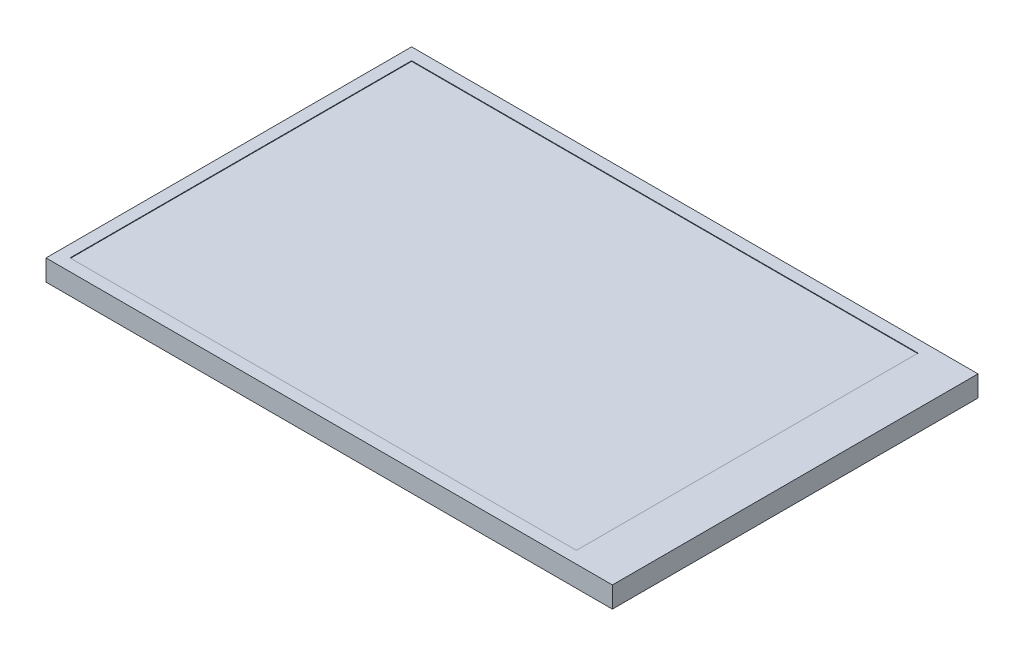
SolidWorks part; units mm, degrees
ref_plane "Front Plane" through (0, 0, 0) normal (0, 0, 1) x (1, 0, 0)
ref_plane "Top Plane" through (0, 0, 0) normal (0, 1, 0) x (1, 0, 0)
ref_plane "Right Plane" through (0, 0, 0) normal (1, 0, 0) x (0, 0, -1)
sketch "Sketch1" plane through (0, 0, 0) normal (0, 1, 0) x (1, 0, 0)
  line L1 (-47.25, 30.5) -> (47.25, 30.5)
  line L2 (-47.25, 30.5) -> (-47.25, -30.5)
  line L3 (-47.25, -30.5) -> (47.25, -30.5)
  line L4 (47.25, 30.5) -> (47.25, -30.5)
  line L5 (-47.25, 30.5) -> (47.25, -30.5) construction
  line L6 (-47.25, -30.5) -> (47.25, 30.5) construction
  point P0 (0, 0)
  dimension "D1" = 94.5
  dimension "D2" = 61
extrude "Boss-Extrude1" add sketch "Sketch1" along normal blind 3.5
sketch "Sketch2" plane through (0, 3.5, 0) normal (0, 1, 0) x (1, 0, 0)
  line L0 (0, 0) -> (-3, 0) construction
  line L2 (-45.25, 28.5) -> (39.25, 28.5)
  line L3 (-45.25, 28.5) -> (-45.25, -28.5)
  line L4 (-45.25, -28.5) -> (39.25, -28.5)
  line L5 (39.25, 28.5) -> (39.25, -28.5)
  line L6 (-45.25, 28.5) -> (39.25, -28.5) construction
  line L7 (-45.25, -28.5) -> (39.25, 28.5) construction
  line L8 (47.25, -30.5) -> (47.25, 30.5) construction
  line L9 (-47.25, 30.5) -> (-47.25, -30.5) construction
  line L10 (-47.25, -30.5) -> (47.25, -30.5) construction
  dimension "D1" = 8
  dimension "D2" = 2
  dimension "D3" = 2
extrude "Cut-Extrude1" cut sketch "Sketch2" against normal blind 0.1
ref_plane "Plane1" through (-3, 0, 0) normal (-1, 0, 0) x (0, 0, 1)
